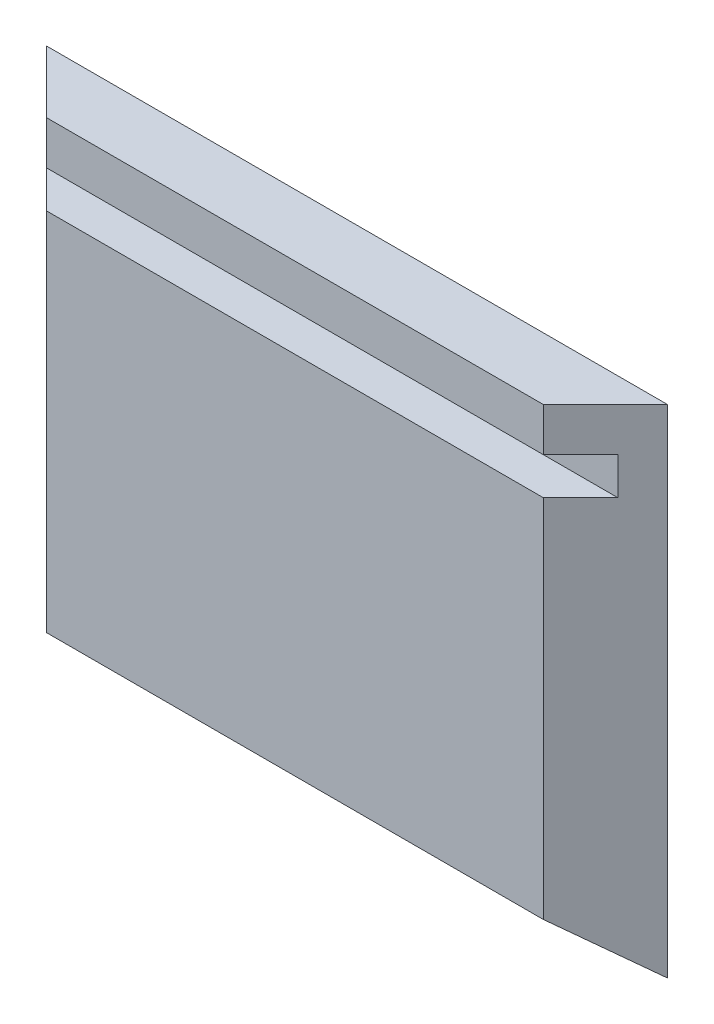
SolidWorks part; units mm, degrees
ref_plane "Front Plane" through (0, 0, 0) normal (0, 0, 1) x (1, 0, 0)
ref_plane "Top Plane" through (0, 0, 0) normal (0, 1, 0) x (1, 0, 0)
ref_plane "Right Plane" through (0, 0, 0) normal (1, 0, 0) x (0, 0, -1)
sketch "Sketch1" plane through (0, 0, 0) normal (0, 0, 1) x (1, 0, 0)
  line L1 (-25, 20) -> (25, 20)
  line L2 (-25, 20) -> (-25, -20)
  line L3 (-25, -20) -> (25, -20)
  line L4 (25, 20) -> (25, -20)
  line L5 (-25, 20) -> (25, -20) construction
  line L6 (-25, -20) -> (25, 20) construction
  point P0 (0, 0)
  dimension "D1" = 40
  dimension "D2" = 50
extrude "Boss-Extrude1" add sketch "Sketch1" along normal blind 5
sketch "Sketch2" plane through (0, 0, 0) normal (0, 1, 0) x (1, 0, 0)
  line L0 (-25, 0) -> (-20, -5)
  line L1 (25, 0) -> (20, -5)
  line L2 (25, 0) -> (-25, 0) construction
  line L3 (-25, -5) -> (-25, 0) construction
  line L4 (-25, -5) -> (-25, 0)
  line L5 (25, -5) -> (-25, -5) construction
  line L6 (25, -5) -> (20, -5)
  line L7 (25, -5) -> (25, 0) construction
  line L8 (25, -5) -> (25, 0)
  line L9 (-20, -5) -> (-25, -5)
  dimension "D1" = 45
  dimension "D2" = 45
extrude "Cut-Extrude1" cut sketch "Sketch2" against normal through all both and the other way through all
sketch "Sketch3" plane through (0, 0, 0) normal (1, 0, 0) x (0, 0, -1)
  line L0 (0, -20) -> (-5, -15.9168)
  line L1 (-5, -20) -> (-5, 20) construction
  line L2 (-5, -20) -> (-5, -15.9168)
  line L3 (0, -20) -> (-5, -20) construction
  line L4 (0, -20) -> (-5, -20)
extrude "Cut-Extrude2" cut sketch "Sketch3" against normal through all both and the other way through all
sketch "Sketch4" plane through (0, 0, 0) normal (1, 0, 0) x (0, 0, -1)
  line L5 (-5, -15.9168) -> (-5, 20) construction
  line L6 (0, 20) -> (-5, 20) construction
  line L11 (0, 20) -> (0, 10) construction
  line L12 (0, 10) -> (-5, 10) construction
  line L13 (-5, 20) -> (-5, 10) construction
  line L14 (-5, 15) -> (0, 15) construction
  line L16 (-5, 16.5) -> (-2, 16.5)
  line L17 (-5, 16.5) -> (-5, 13.5)
  line L18 (-5, 13.5) -> (-2, 13.5)
  line L19 (-2, 16.5) -> (-2, 13.5)
  dimension "D1" = 10
  dimension "D2" = 3
  dimension "D3" = 3
  dimension "D4" = 1.5
extrude "Cut-Extrude3" cut sketch "Sketch4" against normal through all both and the other way through all
